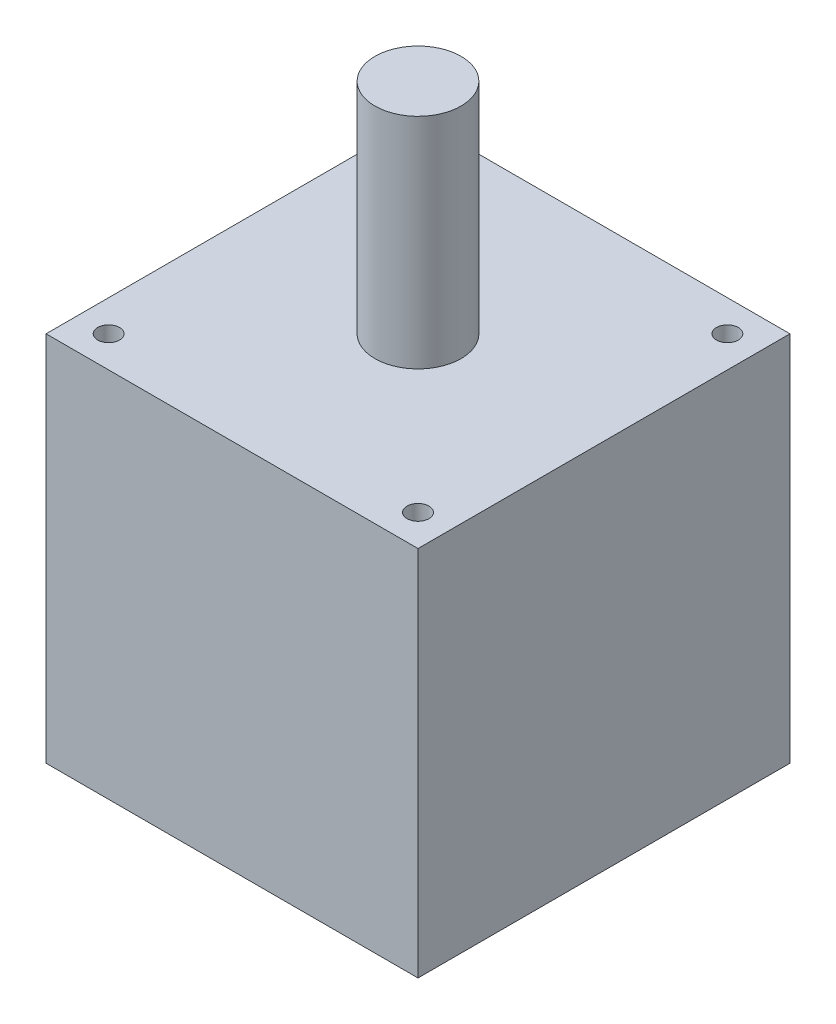
SolidWorks part; units mm, degrees
ref_plane "Front Plane" through (0, 0, 0) normal (0, 0, 1) x (1, 0, 0)
ref_plane "Top Plane" through (0, 0, 0) normal (0, 1, 0) x (1, 0, 0)
ref_plane "Right Plane" through (0, 0, 0) normal (1, 0, 0) x (0, 0, -1)
sketch "Sketch1" plane through (0, 0, 0) normal (0, 1, 0) x (1, 0, 0)
  line L1 (-21.59, -21.59) -> (21.59, -21.59)
  line L2 (-21.59, -21.59) -> (-21.59, 21.59)
  line L3 (-21.59, 21.59) -> (21.59, 21.59)
  line L4 (21.59, -21.59) -> (21.59, 21.59)
  line L5 (-21.59, -21.59) -> (21.59, 21.59) construction
  line L6 (-21.59, 21.59) -> (21.59, -21.59) construction
  point P0 (0, 0)
  dimension "D1" = 43.18
extrude "Boss-Extrude1" add sketch "Sketch1" along normal blind 43.18
sketch "Sketch2" plane through (0, 43.18, 0) normal (0, 1, 0) x (1, 0, 0)
  circle A0 centre (0, 0) radius 5
extrude "Boss-Extrude2" add sketch "Sketch2" along normal blind 25.4
sketch "Sketch3" plane through (0, 43.18, 0) normal (0, 1, 0) x (1, 0, 0)
  line L0 (0, 0) -> (-17.9605, 17.9605) construction
  line L2 (0, 0) -> (36.8461, 0) construction
  line L3 (0, 0) -> (0, 25.8104) construction
  circle A0 centre (-17.9605, 17.9605) radius 1.27
  dimension "D4" = 2.54
  dimension "D1" = 25.4
  dimension "D2" = 135
extrude "Cut-Extrude1" cut sketch "Sketch3" against normal up to surface (43.18 mm away) up to face at (0, 0, 0)
pattern_linear "LPattern1" count 2 spacing 35.9156 along (1, 0, 0) count 2 spacing 35.9156 along (0, 0, 1) of "Cut-Extrude1"
